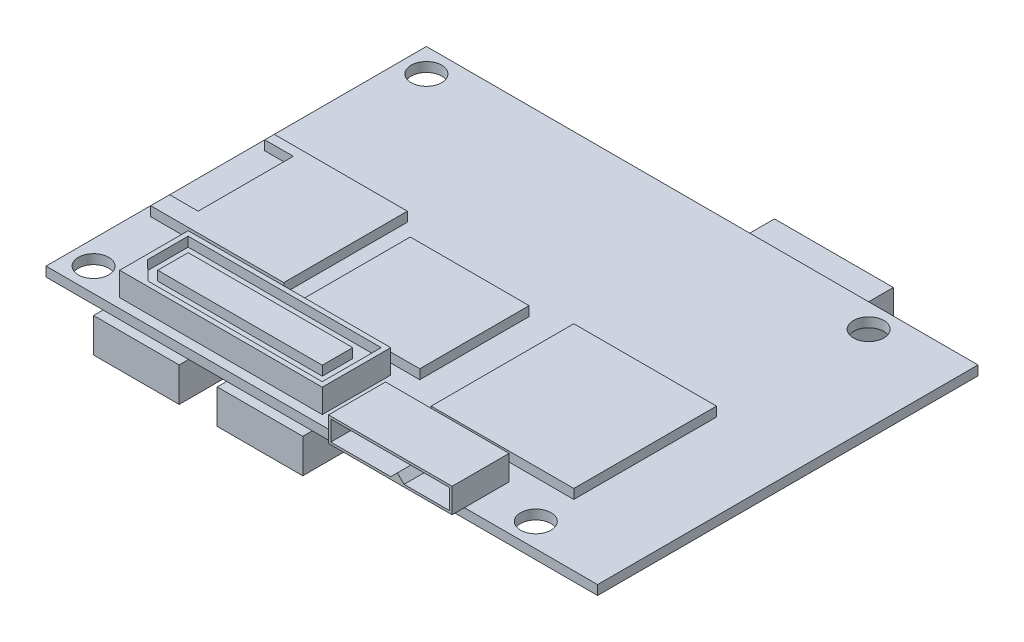
SolidWorks part; units mm, degrees
ref_plane "Front Plane" through (0, 0, 0) normal (0, 0, 1) x (1, 0, 0)
ref_plane "Top Plane" through (0, 0, 0) normal (0, 1, 0) x (1, 0, 0)
ref_plane "Right Plane" through (0, 0, 0) normal (1, 0, 0) x (0, 0, -1)
sketch "Sketch1" plane through (0, 0, 0) normal (0, 1, 0) x (1, 0, 0)
  line L1 (-29, -20) -> (29, -20)
  line L2 (-29, -20) -> (-29, 20)
  line L3 (-29, 20) -> (29, 20)
  line L4 (29, -20) -> (29, 20)
  line L5 (-29, -20) -> (29, 20) construction
  line L6 (-29, 20) -> (29, -20) construction
  point P0 (0, 0)
  dimension "D1" = 40
  dimension "D2" = 58
extrude "Boss-Extrude1" add sketch "Sketch1" along normal blind 1
sketch "Sketch2" plane through (0, 1, 0) normal (0, 1, 0) x (1, 0, 0)
  line L0 (-29, 20) -> (-29, -20) construction
  line L1 (-28, 3) -> (-14, 3)
  line L2 (-28, 3) -> (-28, -10)
  line L3 (-28, -10) -> (-14, -10)
  line L4 (-14, 3) -> (-14, -10)
  line L5 (29, 20) -> (-29, 20) construction
  dimension "D1" = 14
  dimension "D2" = 13
  dimension "D3" = 1
  dimension "D4" = 17
extrude "Boss-Extrude2" add sketch "Sketch2" along normal blind 1
sketch "Sketch3" plane through (0, 2, 0) normal (0, 1, 0) x (1, 0, 0)
  line L0 (-28, 2) -> (-25, 2)
  line L1 (-28, 3) -> (-28, -10) construction
  line L2 (-25, 2) -> (-25, -8)
  line L3 (-25, -8) -> (-28, -8)
  line L4 (-28, 3) -> (-28, -10) construction
  line L5 (-28, 2) -> (-28, -8)
  line L6 (-14, 3) -> (-28, 3) construction
  line L7 (-28, -10) -> (-14, -10) construction
  dimension "D1" = 1
  dimension "D2" = 2
  dimension "D3" = 3
extrude "Cut-Extrude1" cut sketch "Sketch3" against normal blind 1
sketch "Sketch4" plane through (0, 1, 0) normal (0, 1, 0) x (1, 0, 0)
  line L0 (-29, -20) -> (29, -20) construction
  line L1 (-11.5, 0.8) -> (1, 0.8)
  line L2 (-11.5, 0.8) -> (-11.5, -10.7)
  line L3 (-11.5, -10.7) -> (1, -10.7)
  line L4 (1, 0.8) -> (1, -10.7)
  line L5 (5, 1.5) -> (20, 1.5)
  line L6 (5, 1.5) -> (5, -13.5)
  line L7 (5, -13.5) -> (20, -13.5)
  line L8 (20, 1.5) -> (20, -13.5)
  line L9 (-14, -10) -> (-14, 3) construction
  line L10 (29, -20) -> (29, 20) construction
  dimension "D1" = 15
  dimension "D2" = 15
  dimension "D3" = 12.5
  dimension "D4" = 11.5
  dimension "D5" = 9.3
  dimension "D6" = 2.5
  dimension "D7" = 9
  dimension "D8" = 6.5
extrude "Boss-Extrude3" add sketch "Sketch4" along normal blind 1
sketch "Sketch5" plane through (0, 1, 0) normal (0, 1, 0) x (1, 0, 0)
  line L0 (-29, -20) -> (29, -20) construction
  line L1 (2, -15.3) -> (15, -15.3)
  line L2 (2, -15.3) -> (2, -21.3)
  line L3 (2, -21.3) -> (15, -21.3)
  line L4 (15, -15.3) -> (15, -21.3)
  line L5 (29, -20) -> (29, 20) construction
  dimension "D1" = 13
  dimension "D2" = 6
  dimension "D3" = 1.3
  dimension "D4" = 14
extrude "Boss-Extrude4" add sketch "Sketch5" along normal blind 2.6
sketch "Sketch6" plane through (0, 0, 21.3) normal (0, 0, 1) x (1, 0, 0)
  line L0 (2.25, 3.35) -> (14.75, 3.35)
  line L1 (14.75, 3.35) -> (14.75, 1.25)
  line L2 (14.75, 1.25) -> (9.95, 1.25)
  line L3 (9.95, 1.25) -> (9.25, 1.95)
  line L4 (9.25, 1.95) -> (8.55, 1.25)
  line L5 (8.55, 1.25) -> (2.25, 1.25)
  line L6 (2.25, 1.25) -> (2.25, 3.35)
  line L7 (2, 3.6) -> (15, 3.6) construction
  line L8 (2, 3.6) -> (2, 1) construction
  line L9 (15, 3.6) -> (15, 1) construction
  line L10 (2, 1) -> (15, 1) construction
  point P15 (8.741, 1.25)
  dimension "D1" = 0.25
  dimension "D2" = 0.25
  dimension "D3" = 0.25
  dimension "D4" = 0.25
  dimension "D5" = 5.5
  dimension "D6" = 0.7
extrude "Cut-Extrude2" cut sketch "Sketch6" against normal blind 5
sketch "Sketch7" plane through (0, 1, 0) normal (0, 1, 0) x (1, 0, 0)
  line L0 (-29, -20) -> (2, -20) construction
  line L1 (-22.25, -11.8) -> (-0.95, -11.8)
  line L2 (-22.25, -11.8) -> (-22.25, -19)
  line L3 (-22.25, -19) -> (-0.95, -19)
  line L4 (-0.95, -11.8) -> (-0.95, -19)
  line L5 (-29, 20) -> (-29, -20) construction
  dimension "D1" = 21.3
  dimension "D2" = 7.2
  dimension "D3" = 1
  dimension "D4" = 6.75
extrude "Boss-Extrude5" add sketch "Sketch7" along normal blind 2.5
sketch "Sketch8" plane through (0, 3.5, 0) normal (0, 1, 0) x (1, 0, 0)
  line L0 (-22.25, -16.8) -> (-19.95, -19) construction
  line L1 (-20.25, -13.8) -> (-2.95, -13.8)
  line L2 (-20.25, -13.8) -> (-20.25, -17)
  line L3 (-20.25, -17) -> (-2.95, -17)
  line L4 (-2.95, -13.8) -> (-2.95, -17)
  line L5 (-21.75, -12.3) -> (-21.75, -16.5864)
  line L6 (-21.75, -16.5864) -> (-19.7494, -18.5)
  line L7 (-19.7494, -18.5) -> (-1.45, -18.5)
  line L8 (-22.25, -11.8) -> (-22.25, -19)
  line L9 (-22.25, -19) -> (-0.95, -19)
  line L10 (-0.95, -19) -> (-0.95, -11.8)
  line L11 (-0.95, -11.8) -> (-22.25, -11.8)
  line L12 (-22.25, -11.8) -> (-22.25, -16.8) construction
  line L13 (-19.95, -19) -> (-0.95, -19) construction
  line L14 (-0.95, -19) -> (-0.95, -11.8) construction
  line L15 (-0.95, -11.8) -> (-22.25, -11.8) construction
  line L16 (-1.45, -18.5) -> (-1.45, -12.3)
  line L17 (-1.45, -12.3) -> (-21.75, -12.3)
  dimension "D2" = 5
  dimension "D3" = 19
  dimension "D4" = 2
  dimension "D5" = 2
  dimension "D6" = 2
  dimension "D7" = 2
  dimension "D1" = 0
  dimension "D8" = 0.5
extrude "Cut-Extrude3" cut sketch "Sketch8" against normal blind 1
sketch "Sketch9" plane through (0, 1, 0) normal (0, 1, 0) x (1, 0, 0)
  line L0 (0, 0) -> (-50000, 0) construction
  line L1 (-29, 20) -> (-29, -20) construction
  circle A0 centre (-26.5, 17.5) radius 1.6
  circle A1 centre (20, 17.5) radius 1.6
  circle A2 centre (20, -17.5) radius 1.6
  circle A3 centre (-26.5, -17.5) radius 1.6
  point P8 (0, 0)
  point P14 (0, 0)
  point P15 (0, 0)
  point P16 (0, 0)
  dimension "D1" = 46.5
  dimension "D3" = 3.2
  dimension "D2" = 35
  dimension "D4" = 2.5
extrude "Cut-Extrude4" cut sketch "Sketch9" against normal through all
sketch "Sketch10" plane through (0, 0, 0) normal (0, -1, 0) x (1, 0, 0)
  line L0 (-29, -20) -> (-29, 20) construction
  line L1 (-23, 21) -> (-14, 21)
  line L2 (-23, 21) -> (-23, 16)
  line L3 (-23, 16) -> (-14, 16)
  line L4 (-14, 21) -> (-14, 16)
  line L5 (-10, 21) -> (-1, 21)
  line L6 (-10, 21) -> (-10, 16)
  line L7 (-10, 16) -> (-1, 16)
  line L8 (-1, 21) -> (-1, 16)
  line L9 (-22.3, -21) -> (-13.3, -21)
  line L10 (-22.3, -21) -> (-22.3, -16)
  line L11 (-22.3, -16) -> (-13.3, -16)
  line L12 (-13.3, -21) -> (-13.3, -16)
  line L13 (-9.3, -21) -> (-0.3, -21)
  line L14 (-9.3, -21) -> (-9.3, -16)
  line L15 (-9.3, -16) -> (-0.3, -16)
  line L16 (-0.3, -21) -> (-0.3, -16)
  line L17 (-29, 20) -> (29, 20) construction
  line L18 (29, -20) -> (-29, -20) construction
  dimension "D1" = 9
  dimension "D2" = 5
  dimension "D3" = 6
  dimension "D4" = 4
  dimension "D5" = 1
  dimension "D6" = 1
  dimension "D7" = 4
  dimension "D8" = 6.7
extrude "Boss-Extrude6" add sketch "Sketch10" along normal blind 3.6
sketch "Sketch11" plane through (0, 0, 0) normal (0, -1, 0) x (1, 0, 0)
  line L0 (29, -20) -> (-0.3, -20) construction
  line L1 (4, -17.35) -> (16.5, -17.35)
  line L2 (4, -17.35) -> (4, -23.6)
  line L3 (4, -23.6) -> (16.5, -23.6)
  line L4 (16.5, -17.35) -> (16.5, -23.6)
  line L5 (29, 20) -> (29, -20) construction
  dimension "D1" = 6.25
  dimension "D2" = 3.6
  dimension "D3" = 12.5
  dimension "D4" = 12.5
extrude "Boss-Extrude7" add sketch "Sketch11" along normal blind 5
sketch "Sketch12" plane through (0, 0, 0) normal (0, -1, 0) x (1, 0, 0)
  line L0 (-29, -20) -> (-29, 20) construction
  line L1 (-23, 11.5) -> (-13, 11.5)
  line L2 (-23, 11.5) -> (-23, 1.5)
  line L3 (-23, 1.5) -> (-13, 1.5)
  line L4 (-13, 11.5) -> (-13, 1.5)
  line L5 (-29, 20) -> (-23, 20) construction
  dimension "D1" = 10
  dimension "D2" = 6
  dimension "D3" = 8.5
extrude "Boss-Extrude8" add sketch "Sketch12" along normal blind 2.5
sketch "Sketch13" plane through (0, 0, 0) normal (0, -1, 0) x (1, 0, 0)
  line L0 (-29, 20) -> (-23, 20) construction
  line L1 (-29, -20) -> (-29, 20) construction
  circle A0 centre (-26.5, 12.5) radius 1
  circle A1 centre (-26.5, 4) radius 1
  circle A2 centre (-26.5, -3.5) radius 1
  circle A3 centre (-26.5, 12.5) radius 0.8
  circle A4 centre (-26.5, 4) radius 0.8
  circle A5 centre (-26.5, -3.5) radius 0.8
  point P10 (0, 0)
  dimension "D1" = 2
  dimension "D2" = 7.5
  dimension "D3" = 8.5
  dimension "D4" = 7.5
  dimension "D5" = 2.5
  dimension "D6" = 0.2
  dimension "D7" = 0.2
  dimension "D8" = 0.2
extrude "Boss-Extrude9" add sketch "Sketch13" along normal blind 1
sketch "Sketch14" plane through (0, 0, 0) normal (0, -1, 0) x (1, 0, 0)
  circle A0 centre (-26.5, 12.5) radius 0.15
  circle A1 centre (-26.5, 4) radius 0.15
  circle A2 centre (-26.5, -3.5) radius 0.15
  dimension "D1" = 0.3
extrude "Boss-Extrude10" add sketch "Sketch14" along normal blind 1
